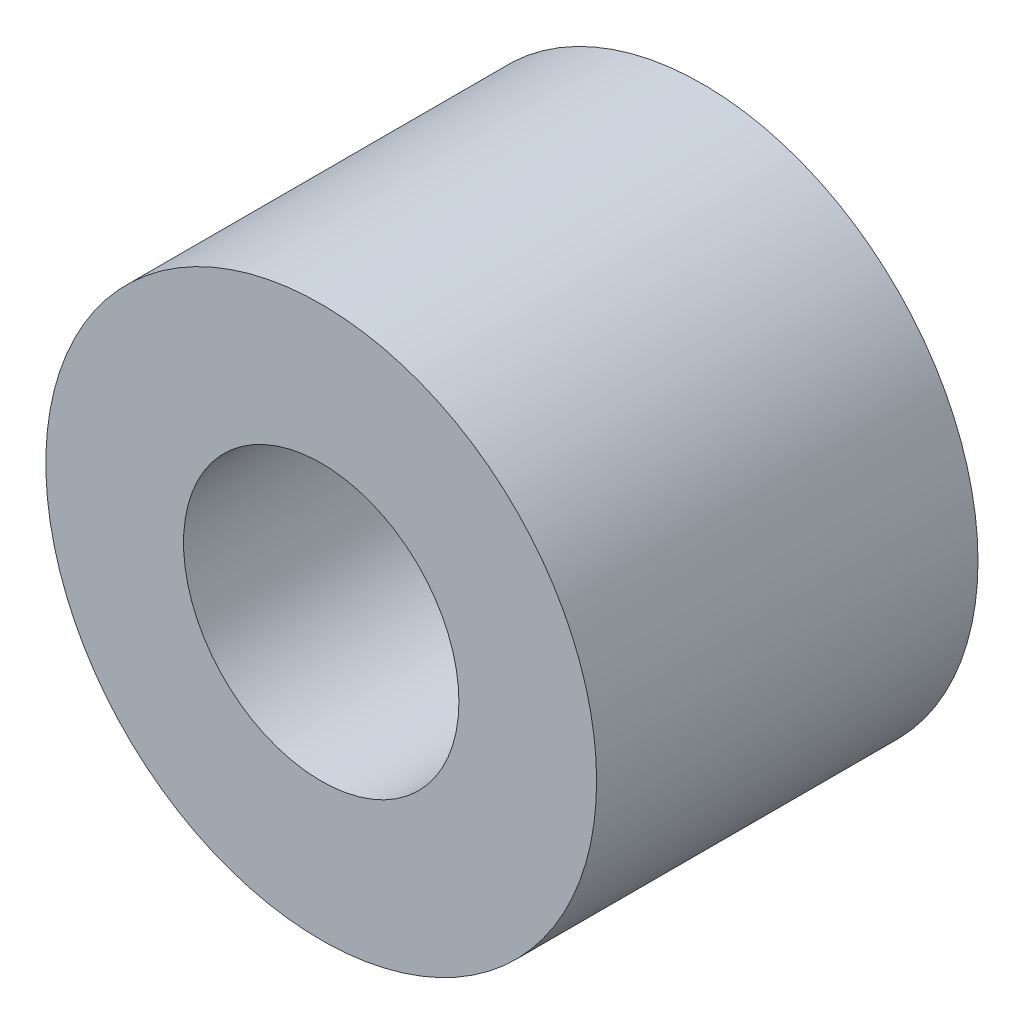
SolidWorks part; units mm, degrees
ref_plane "Front Plane" through (0, 0, 0) normal (0, 0, 1) x (1, 0, 0)
ref_plane "Top Plane" through (0, 0, 0) normal (0, 1, 0) x (1, 0, 0)
ref_plane "Right Plane" through (0, 0, 0) normal (1, 0, 0) x (0, 0, -1)
sketch "Sketch1" plane through (0, 0, 0) normal (0, 0, 1) x (1, 0, 0)
  circle A0 centre (0, 0) radius 6.35
  circle A1 centre (0, 0) radius 3.175
  dimension "D1" = 6.35
  dimension "D2" = 12.7
extrude "Boss-Extrude1" add sketch "Sketch1" along normal blind 8.7937
